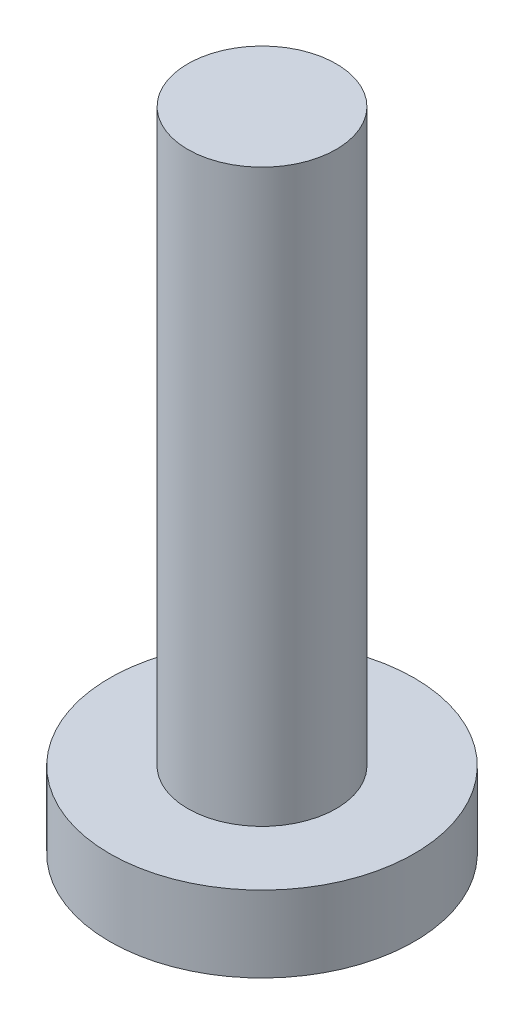
SolidWorks part; units mm, degrees
ref_plane "Front Plane" through (0, 0, 0) normal (0, 0, 1) x (1, 0, 0)
ref_plane "Top Plane" through (0, 0, 0) normal (0, 1, 0) x (1, 0, 0)
ref_plane "Right Plane" through (0, 0, 0) normal (1, 0, 0) x (0, 0, -1)
sketch "Sketch1" plane through (0, 0, 0) normal (0, 1, 0) x (1, 0, 0)
  circle A0 centre (0, 0) radius 4
  dimension "D1" = 8
extrude "Boss-Extrude1" add sketch "Sketch1" against normal blind 2
sketch "Sketch2" plane through (0, 0, 0) normal (0, 1, 0) x (1, 0, 0)
  circle A0 centre (0, 0) radius 1.95
  dimension "D1" = 3.9
extrude "Boss-Extrude2" add sketch "Sketch2" along normal blind 15
